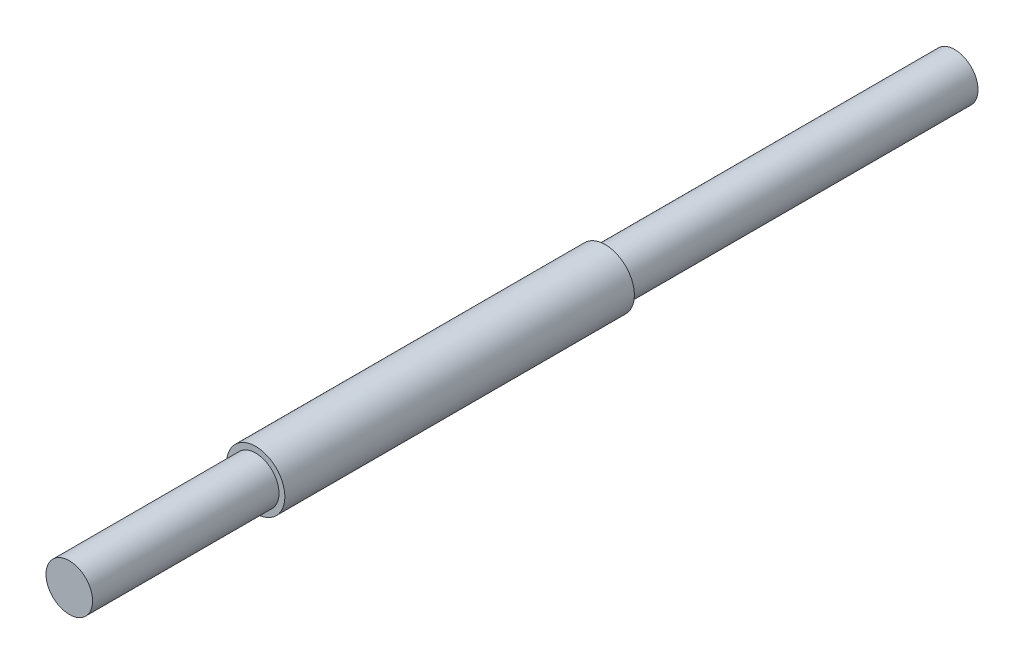
SolidWorks part; units mm, degrees
ref_plane "Alzado" through (0, 0, 0) normal (0, 0, 1) x (1, 0, 0)
ref_plane "Planta" through (0, 0, 0) normal (0, 1, 0) x (1, 0, 0)
ref_plane "Vista lateral" through (0, 0, 0) normal (1, 0, 0) x (0, 0, -1)
sketch "Croquis1" plane through (0, 0, 0) normal (0, 0, 1) x (1, 0, 0)
  circle A0 centre (0, 0) radius 10
  dimension "D1" = 20
extrude "Saliente-Extruir1" add sketch "Croquis1" along normal blind 80
sketch "Croquis2" plane through (0, 0, 0) normal (0, 0, -1) x (-1, 0, 0)
  circle A0 centre (0, 0) radius 12.5
  dimension "D1" = 25
extrude "Saliente-Extruir2" add sketch "Croquis2" along normal blind 150
sketch "Croquis3" plane through (0, 0, -150) normal (0, 0, -1) x (-1, 0, 0)
  circle A0 centre (0, 0) radius 10
  dimension "D1" = 20
extrude "Saliente-Extruir3" add sketch "Croquis3" along normal blind 150
